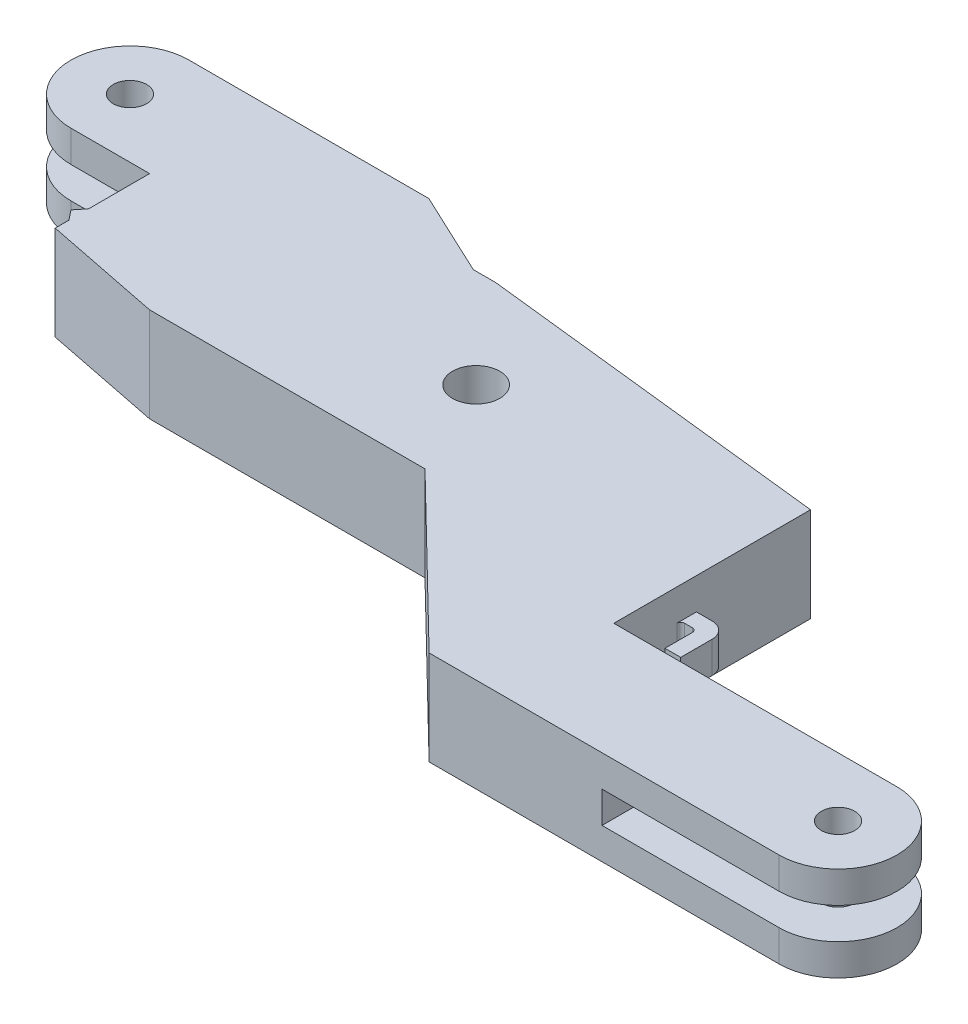
SolidWorks part; units mm, degrees
ref_plane "Front Plane" through (0, 0, 0) normal (0, 0, 1) x (1, 0, 0)
ref_plane "Top Plane" through (0, 0, 0) normal (0, 1, 0) x (1, 0, 0)
ref_plane "Right Plane" through (0, 0, 0) normal (1, 0, 0) x (0, 0, -1)
sketch "Sketch1" plane through (0, 0, 0) normal (0, 1, 0) x (1, 0, 0)
  line L1 (0, -7.5) -> (10, -7.5)
  line L2 (10, -7.5) -> (10, -22.5) construction
  line L3 (10, -22.5) -> (60, -22.5)
  line L5 (30.4808, 7.5) -> (0, 7.5)
  line L8 (60, -22.5) -> (80.5222, -42.5)
  line L9 (80.5222, -42.5) -> (125, -42.5)
  line L11 (125, -27.5) -> (89, -27.5)
  line L12 (89, -27.5) -> (89, 2.5)
  line L13 (41.1412, 2.5) -> (89, 2.5)
  line L14 (30.4808, 7.5) -> (41.1412, 2.5)
  arc A0 (0, 7.5) -> (0, -7.5) centre (0, 0) ccw
  circle A1 centre (0, 0) radius 2.125
  circle A3 centre (125, -35) radius 2.125
  arc A4 (125, -42.5) -> (125, -27.5) centre (125, -35) ccw
  circle A5 centre (54, -10) radius 3
  dimension "D1" = 4.25
  dimension "D2" = 15
  dimension "D3" = 4.25
  dimension "D7" = 15
  dimension "D10" = 6
  dimension "D4" = 10
  dimension "D5" = 50
  dimension "D6" = 25
  dimension "D8" = 125
  dimension "D9" = 5
  dimension "D11" = 12.5
  dimension "D12" = 6
  dimension "D13" = 35
  dimension "D14" = 5
extrude "Boss-Extrude1" add sketch "Sketch1" along normal blind 12
sketch "Sketch2" plane through (0, 0, -7.5) normal (0, 0, -1) x (-1, 0, 0)
  line L0 (-12.5, 0) -> (-12.5, 12) construction
  line L1 (-30.4808, 0) -> (0, 0) construction
  line L2 (-30.4808, 12) -> (0, 12) construction
  line L3 (7.5, 0) -> (7.5, 12) construction
  line L4 (-32.5, 8) -> (7.5, 8)
  line L5 (-32.5, 8) -> (-32.5, 4)
  line L6 (-32.5, 4) -> (7.5, 4)
  line L7 (7.5, 8) -> (7.5, 4)
  line L8 (-32.5, 8) -> (7.5, 4) construction
  line L9 (-32.5, 4) -> (7.5, 8) construction
  point P6 (-12.5, 6)
  dimension "D1" = 4
  dimension "D2" = 40
extrude "Slot1 Cut" cut sketch "Sketch2" against normal up to surface (15 mm away) up to face at (5, 6, 7.5)
sketch "Sketch3" plane through (0, 0, 27.5) normal (0, 0, -1) x (-1, 0, 0)
  line L0 (-117.5, 0) -> (-117.5, 12) construction
  line L1 (-125, 0) -> (-89, 0) construction
  line L2 (-125, 12) -> (-89, 12) construction
  line L3 (-132.5, 12) -> (-132.5, 0) construction
  line L4 (-102.5, 8) -> (-132.5, 8)
  line L5 (-102.5, 8) -> (-102.5, 4)
  line L6 (-102.5, 4) -> (-132.5, 4)
  line L7 (-132.5, 8) -> (-132.5, 4)
  line L8 (-102.5, 8) -> (-132.5, 4) construction
  line L9 (-102.5, 4) -> (-132.5, 8) construction
  point P6 (-117.5, 6)
  dimension "D1" = 4
  dimension "D2" = 15
extrude "Slot2 Cut" cut sketch "Sketch3" against normal through all
sketch "Sketch4" plane through (0, 12, 0) normal (0, 1, 0) x (1, 0, 0)
  line L1 (10, -19.5) -> (10, -22.5)
  line L3 (10, -7.5) -> (10, -22.5) construction
  line L5 (44, 2.5) -> (89, 2.5)
  line L6 (41.1412, 2.5) -> (89, 2.5) construction
  line L7 (89, 2.5) -> (89, -2.5)
  line L8 (89, -27.5) -> (89, 2.5) construction
  line L10 (44, 2.5) -> (89, -2.5)
  line L11 (10, -22.5) -> (25, -22.5)
  line L12 (10, -22.5) -> (60, -22.5) construction
  line L13 (25, -22.5) -> (10, -19.5)
  dimension "D1" = 3
  dimension "D2" = 5
  dimension "D3" = 45
  dimension "D4" = 15
extrude "Cut-Extrude3" cut sketch "Sketch4" against normal through all
sketch "Sketch5" plane through (89, 0, 0) normal (1, 0, 0) x (0, 0, -1)
  line L0 (2.5, 12) -> (2.5, 0) construction
  line L1 (2.5, 6) -> (-42.5, 6) construction
  line L4 (-17, 4) -> (-23, 4)
  line L5 (-17, 4) -> (-17, 8)
  line L6 (-17, 8) -> (-23, 8)
  line L7 (-23, 4) -> (-23, 8)
  line L8 (-17, 4) -> (-23, 8) construction
  line L9 (-17, 8) -> (-23, 4) construction
  line L10 (2.5, 12) -> (2.5, 0) construction
  point P7 (2.5, 6)
  point P8 (-20, 6)
  dimension "D1" = 4
  dimension "D2" = 6
  dimension "D3" = 22.5
extrude "Boss-Extrude2" add sketch "Sketch5" along normal blind 4 contours L5 L4 L7 L6
sketch "Sketch6" plane through (0, 8, 0) normal (0, 1, 0) x (1, 0, 0)
  line L0 (93, -23) -> (89, -23) construction
  line L1 (89, -17) -> (89, -23) construction
  line L2 (91, -23) -> (89, -23)
  line L3 (91, -23) -> (91, -19.5)
  line L4 (90.5, -19) -> (89.5, -19)
  line L5 (89, -23) -> (89, -19.5)
  line L9 (91, -17) -> (93, -17)
  line L11 (93, -19) -> (93, -17)
  arc A0 (91, -19.5) -> (90.5, -19) centre (90.5, -19.5) ccw
  arc A1 (89.5, -19) -> (89, -19.5) centre (89.5, -19.5) ccw
  arc A3 (93, -19) -> (91, -17) centre (91, -19) ccw
  point P13 (89, -19)
  point P22 (93, -17)
  dimension "D2" = 0.5
  dimension "D3" = 0.5
  dimension "D4" = 2
  dimension "D1" = 4
extrude "Cut-Extrude4" cut sketch "Sketch6" against normal blind 4
sketch "Sketch7" plane through (10, 0, 0) normal (-1, 0, 0) x (0, 0, 1)
  line L0 (17.75, 0) -> (17.75, 12)
  line L1 (7.5, 0) -> (19.5, 0) construction
  line L2 (7.5, 12) -> (19.5, 12) construction
  line L3 (17.75, 12) -> (15.25, 12)
  line L4 (15.25, 12) -> (15.25, 0)
  line L5 (15.25, 0) -> (17.75, 0)
  point P7 (14.3973, 0)
  dimension "D1" = 2.5
  dimension "D2" = 1.75
extrude "Boss-Extrude3" add sketch "Sketch7" along normal blind 1
sketch "Sketch8" plane through (0, 12, 0) normal (0, 1, 0) x (1, 0, 0)
  line L0 (10, -15.25) -> (10, -17.75) construction
  line L1 (10, -15.25) -> (9, -15.25)
  line L2 (9, -15.25) -> (9, -17.75)
  line L3 (10, -17.75) -> (9, -17.75)
  line L5 (10, -17.75) -> (9, -16.5)
  line L6 (9, -16.5) -> (10, -15.25)
  line M8 (10, -15.25) -> (9, -15.25)
  line M9 (9, -15.25) -> (9, -17.75)
  line M10 (9, -17.75) -> (10, -17.75)
extrude "Cut-Extrude5" cut sketch "Sketch8" against normal through all contours L6 M9 M8 | L5 L2 M10
